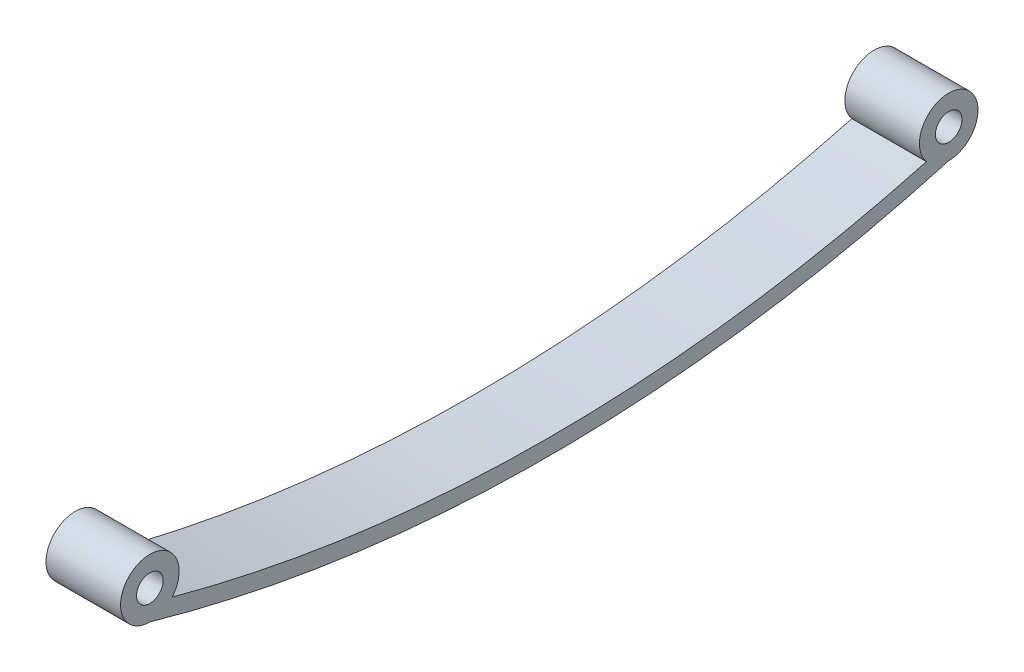
SolidWorks part; units mm, degrees
ref_plane "Front Plane" through (0, 0, 0) normal (0, 0, 1) x (1, 0, 0)
ref_plane "Top Plane" through (0, 0, 0) normal (0, 1, 0) x (1, 0, 0)
ref_plane "Right Plane" through (0, 0, 0) normal (1, 0, 0) x (0, 0, -1)
sketch "Sketch1" plane through (0, 0, 0) normal (1, 0, 0) x (0, 0, -1)
  line L0 (-37.5, 0) -> (37.5, 0) construction
  circle A0 centre (-37.5, 0) radius 1.25
  circle A1 centre (37.5, 0) radius 1.25
  arc A2 (-35.4017, -1.7775) -> (-37.5, -2.75) centre (-37.5, 0) ccw
  arc A3 (37.5, -2.75) -> (35.4017, -1.7775) centre (37.5, 0) ccw
  arc A4 (-37.5, -2.75) -> (37.5, -2.75) centre (0, 128.5536) ccw
  arc A5 (-35.4017, -1.7775) -> (35.4017, -1.7775) centre (0, 128.5536) ccw
  arc A7 (-37.0881, -1.3077) -> (37.0881, -1.3077) centre (0, 128.5536) ccw construction
  circle A8 centre (-37.5, 0) radius 2.75 construction
  circle A9 centre (37.5, 0) radius 2.75 construction
  point P6 (40.25, 0)
  point P12 (0, -8)
  point P18 (-34.75, 0)
  dimension "D3" = 2.5
  dimension "D4" = 2.5
  dimension "D1" = 75
  dimension "D2" = 37.5
  dimension "D6" = 8
  dimension "D5" = 1.5
  dimension "D7" = 1.5
extrude "Boss-Extrude1" add sketch "Sketch1" along normal blind 7
sketch "Sketch4" plane through (0, 0, 0) normal (0, 1, 0) x (1, 0, 0)
  line L0 (0, 0) -> (7, 0) construction
  line L1 (7, -35.4017) -> (7, 35.4017) construction
